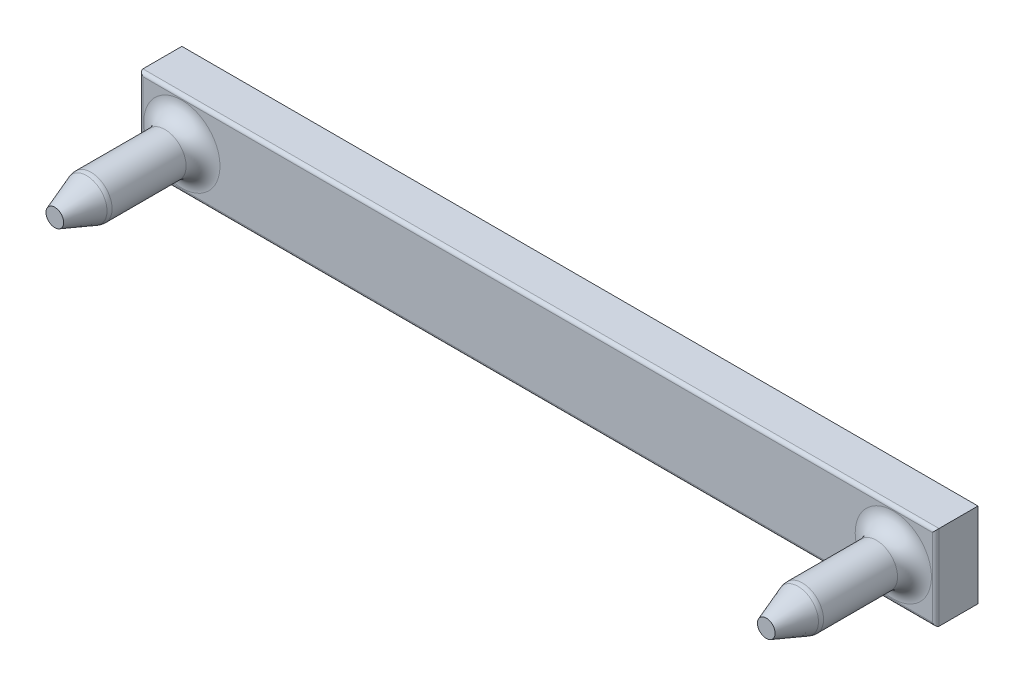
SolidWorks part; units mm, degrees
ref_plane "Ön Düzlem" through (0, 0, 0) normal (1, 0, 0) x (0, 1, 0)
ref_plane "Üst Düzlem" through (0, 0, 0) normal (0, 0, 1) x (0, 1, 0)
ref_plane "Sağ Düzlem" through (0, 0, 0) normal (0, 1, 0) x (-1, 0, 0)
sketch "Sketch1" plane through (0, 0, 0) normal (0, 0, 1) x (0, 1, 0)
  line L1 (0, 0) -> (100, 0)
  line L2 (0, 0) -> (0, 100)
  line L3 (0, 100) -> (100, 100)
  line L4 (100, 0) -> (100, 100)
  dimension "D1" = 100
  dimension "D2" = 100
sketch "Sketch2" plane through (0, 0, 0) normal (0, 0, 1) x (0, 1, 0)
  line L17 (8, 8) -> (92, 8)
  line L18 (92, 8) -> (92, 92)
  line L19 (8, 92) -> (8, 8)
  line L20 (92, 92) -> (8, 92)
  line L21 (8, 8) -> (92, 8) construction
  line L22 (92, 8) -> (92, 92) construction
  line L23 (8, 92) -> (8, 8) construction
  line L24 (92, 92) -> (8, 92) construction
  circle A0 centre (8, 92) radius 2.5
  circle A1 centre (92, 92) radius 2.5 construction
  circle A2 centre (8, 8) radius 2.5
  circle A3 centre (92, 8) radius 2.5 construction
  point P3 (92, 91.1525)
  point P5 (8, 7.0642)
  point P7 (92.8672, 8)
  dimension "D2" = 5
  dimension "D1" = 8
extrude "Boss-Extrude1" add sketch "Sketch2" against normal blind 15
sketch "Sketch3" plane through (0, 0, -15) normal (0, 0, -1) x (1, 0, 0)
  line L0 (-97, -3) -> (-97, -13)
  line L1 (-3, -13) -> (-3, -3)
  line L4 (-97, -3) -> (-3, -3)
  line L9 (-97, -13) -> (-3, -13)
  arc A0 (-94.5008, -8) -> (-92, -10.5008) centre (-92, -8) ccw construction
  dimension "D1" = 5.0016
  dimension "D2" = 5
  dimension "D3" = 5
extrude "Boss-Extrude2" add sketch "Sketch3" along normal blind 5
sketch "Sketch4" plane through (0, 0, -20) normal (0, 0, -1) x (1, 0, 0)
  line L1 (-87, -13.4) -> (-81, -13.4)
  line L4 (-87, -20) -> (-87, -19.99)
  line L6 (0, 0) -> (-100, 0) construction
  line L7 (-89, 0) -> (-98, 0)
  line L9 (-97.5, -16) -> (-98, -16)
  line L10 (-100, 0) -> (-100, -100) construction
  line L11 (-100, -14) -> (-100, -2)
  line L12 (-50, 0) -> (-50, -100) construction
  line L13 (-81, -13.4) -> (-81, -14.01)
  line L14 (-87, -20) -> (-87, -80)
  line L15 (-100, -50) -> (8.7692, -50) construction
  line L16 (-97.4, -13.4) -> (-87, -13.4)
  line L17 (-93.5, -20) -> (-93.5, -80)
  line L18 (-97.4, -2.6) -> (-97.4, -13.4)
  line L19 (-97.4, -2.6) -> (-87, -2.6)
  line L20 (-87, -2.6) -> (-87, -2)
  line L21 (-81, -85.99) -> (-81, -86)
  line L24 (-83.01, -16) -> (-83, -16)
  line L26 (-83, -16) -> (-82.99, -16)
  line L29 (-81, -14.01) -> (-81, -14)
  line L30 (-83, -84) -> (-82.99, -84)
  line L31 (-83.01, -84) -> (-83, -84)
  line L32 (-87, -97.4) -> (-87, -98)
  line L33 (-97.4, -97.4) -> (-87, -97.4)
  line L34 (-97.4, -97.4) -> (-97.4, -86.6)
  line L35 (-97.4, -86.6) -> (-87, -86.6)
  line L36 (-81, -86.6) -> (-81, -85.99)
  line L37 (-100, -86) -> (-100, -98)
  line L38 (-97.5, -84) -> (-98, -84)
  line L39 (-89, -100) -> (-98, -100)
  line L40 (-87, -80) -> (-87, -80.01)
  line L41 (-87, -86.6) -> (-81, -86.6)
  arc A0 (-97.5, -16) -> (-93.5, -20) centre (-97.5, -20) cw
  arc A1 (-87, -2) -> (-89, 0) centre (-89, -2) ccw
  arc A2 (-98, 0) -> (-100, -2) centre (-98, -2) ccw
  arc A3 (-98, -16) -> (-100, -14) centre (-98, -14) cw
  arc A4 (-87, -19.99) -> (-83.01, -16) centre (-83.01, -19.99) cw
  arc A5 (-82.99, -16) -> (-81, -14.01) centre (-82.99, -14.01) ccw
  arc A6 (-82.99, -84) -> (-81, -85.99) centre (-82.99, -85.99) cw
  arc A7 (-87, -80.01) -> (-83.01, -84) centre (-83.01, -80.01) ccw
  arc A8 (-98, -84) -> (-100, -86) centre (-98, -86) ccw
  arc A9 (-98, -100) -> (-100, -98) centre (-98, -98) cw
  arc A10 (-87, -98) -> (-89, -100) centre (-89, -98) cw
  arc A11 (-97.5, -84) -> (-93.5, -80) centre (-97.5, -80) ccw
  point P7 (-87, 0)
  point P11 (-100, 0)
  point P25 (-100, -16)
  point P63 (-93.5, -50)
  point P65 (-87, -50)
  point P66 (-100, -84)
  point P67 (-100, -100)
  point P68 (-87, -100)
  dimension "D1" = 4
  dimension "D2" = 2
  dimension "D3" = 3.99
  dimension "D4" = 1.99
fillet "Fillet1" radius 2 2 edges at (-5.5, 8, -15) (-89.5, 8, -15)
fillet "Fillet2" radius 0.4 4 edges at (-3, 8, -15) (-50, 13, -15) (-97, 8, -15) (-50, 3, -15)
chamfer "Chamfer1" distance 4 angle 20 2 edges at (-5.5, 8, 0) (-89.5, 8, 0)
fillet "Fillet4" radius 1.5 2 edges at (-5.5, 8, -4) (-89.5, 8, -4)
